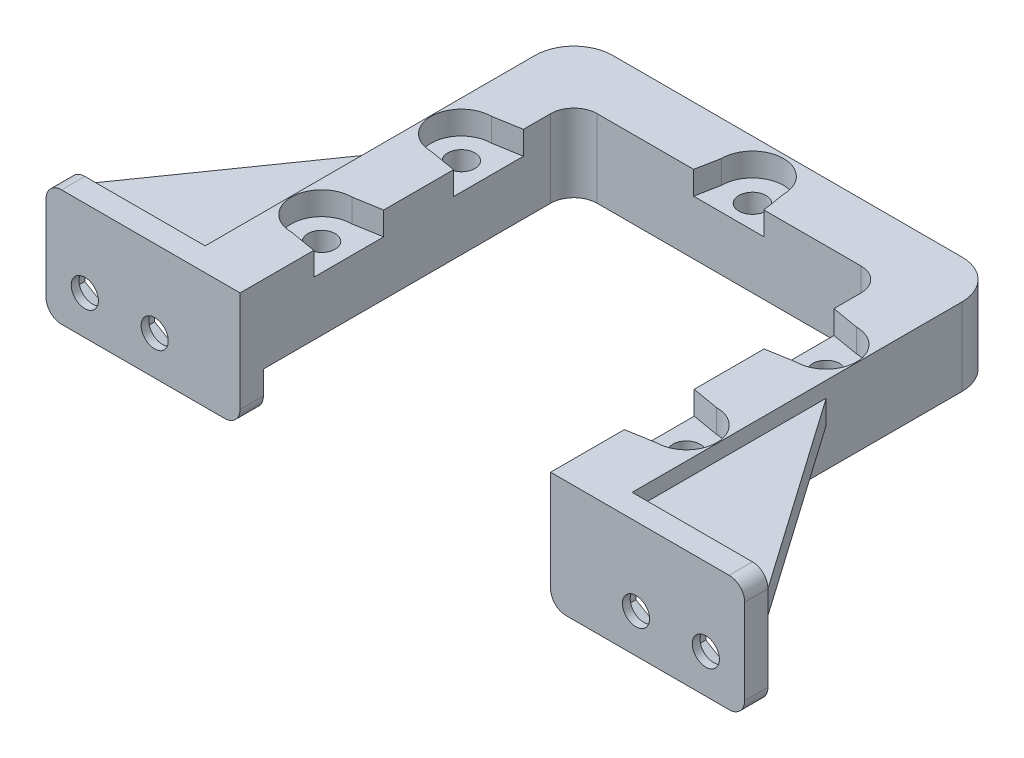
SolidWorks part; units mm, degrees
ref_plane "Front Plane" through (0, 0, 0) normal (0, 0, 1) x (1, 0, 0)
ref_plane "Top Plane" through (0, 0, 0) normal (0, 1, 0) x (1, 0, 0)
ref_plane "Right Plane" through (0, 0, 0) normal (1, 0, 0) x (0, 0, -1)
sketch "Sketch1" plane through (0, 0, 0) normal (0, 1, 0) x (1, 0, 0)
  line L0 (-20, -20) -> (-27.5, -20)
  line L1 (-17, 20) -> (17, 20)
  line L2 (-20, 17) -> (-20, -20)
  line L4 (20, 17) -> (20, -20)
  line L5 (-20, 20) -> (20, -20) construction
  line L6 (-20, -20) -> (20, 20) construction
  line L7 (-22.5, 27.5) -> (22.5, 27.5)
  line L8 (-27.5, 22.5) -> (-27.5, -20)
  line L10 (27.5, 22.5) -> (27.5, -20)
  line L11 (-27.5, 27.5) -> (27.5, -27.5) construction
  line L12 (-27.5, -27.5) -> (27.5, 27.5) construction
  line L13 (20, -20) -> (27.5, -20)
  line L14 (-20, -20) -> (20, -20) construction
  arc A0 (17, 20) -> (20, 17) centre (17, 17) cw
  arc A1 (-17, 20) -> (-20, 17) centre (-17, 17) ccw
  arc A2 (22.5, 27.5) -> (27.5, 22.5) centre (22.5, 22.5) cw
  arc A3 (-22.5, 27.5) -> (-27.5, 22.5) centre (-22.5, 22.5) ccw
  point P0 (0, 0)
  point P12 (0, 0)
  dimension "D3" = 3
  dimension "D6" = 5
  dimension "D1" = 40
  dimension "D2" = 40
  dimension "D4" = 55
  dimension "D5" = 55
  dimension "D9" = 7.5
extrude "Boss-Extrude1" add sketch "Sketch1" along normal blind 10
sketch "Sketch2" plane through (0, 10, 0) normal (0, 1, 0) x (1, 0, 0)
  line L0 (-23.5, -9) -> (23.5, -9) construction
  line L1 (0, -9) -> (0, -20) construction
  line L4 (-20, -20) -> (20, -20) construction
  line L5 (0, 20) -> (0, 23) construction
  line L6 (-17, 20) -> (17, 20) construction
  line L7 (-23.5, 9) -> (23.5, 9) construction
  line L8 (0, 9) -> (0, 20) construction
  circle A0 centre (-23.5, -9) radius 1.75
  circle A1 centre (23.5, -9) radius 1.75
  circle A2 centre (0, 23) radius 1.75
  circle A3 centre (-23.5, 9) radius 1.75
  circle A4 centre (23.5, 9) radius 1.75
  dimension "D3" = 3.5
  dimension "D4" = 3.5
  dimension "D6" = 3.5
  dimension "D9" = 3.5
  dimension "D10" = 3.5
  dimension "D1" = 11
  dimension "D2" = 47
  dimension "D5" = 3
  dimension "47" = 47
  dimension "D8" = 11
extrude "Cut-Extrude1" cut sketch "Sketch2" against normal blind 15.5
sketch "Sketch3" plane through (0, 0, 0) normal (0, -1, 0) x (1, 0, 0)
  line L1 (-20.6, 7.3257) -> (-20.6, 10.6743)
  line L2 (-20.6, 10.6743) -> (-23.5, 12.3486)
  line L3 (-23.5, 12.3486) -> (-26.4, 10.6743)
  line L4 (-26.4, 10.6743) -> (-26.4, 7.3257)
  line L5 (-26.4, 7.3257) -> (-23.5, 5.6514)
  line L6 (-23.5, 5.6514) -> (-20.6, 7.3257)
  line L7 (23.4997, 5.6514) -> (26.3998, 7.3254)
  line L8 (26.3998, 7.3254) -> (26.4002, 10.674)
  line L9 (26.4002, 10.674) -> (23.5003, 12.3486)
  line L10 (23.5003, 12.3486) -> (20.6002, 10.6746)
  line L11 (20.6002, 10.6746) -> (20.5998, 7.326)
  line L12 (20.5998, 7.326) -> (23.4997, 5.6514)
  line L13 (3.3486, -23) -> (1.6743, -20.1)
  line L14 (1.6743, -20.1) -> (-1.6743, -20.1)
  line L15 (-1.6743, -20.1) -> (-3.3486, -23)
  line L16 (-3.3486, -23) -> (-1.6743, -25.9)
  line L17 (-1.6743, -25.9) -> (1.6743, -25.9)
  line L18 (1.6743, -25.9) -> (3.3486, -23)
  line L19 (-23.4997, -5.6514) -> (-26.3998, -7.3254)
  line L20 (-26.3998, -7.3254) -> (-26.4002, -10.674)
  line L21 (-26.4002, -10.674) -> (-23.5003, -12.3486)
  line L22 (-23.5003, -12.3486) -> (-20.6002, -10.6746)
  line L23 (-20.6002, -10.6746) -> (-20.5998, -7.326)
  line L24 (-20.5998, -7.326) -> (-23.4997, -5.6514)
  line L25 (23.4997, -5.6514) -> (20.5998, -7.326)
  line L26 (20.5998, -7.326) -> (20.6002, -10.6746)
  line L27 (20.6002, -10.6746) -> (23.5003, -12.3486)
  line L28 (23.5003, -12.3486) -> (26.4002, -10.674)
  line L29 (26.4002, -10.674) -> (26.3998, -7.3254)
  line L30 (26.3998, -7.3254) -> (23.4997, -5.6514)
  circle A0 centre (-23.5, 9) radius 2.9 construction
  circle A1 centre (23.5, 9) radius 2.9 construction
  circle A2 centre (0, -23) radius 2.9 construction
  circle A3 centre (-23.5, -9) radius 2.9 construction
  circle A4 centre (23.5, -9) radius 2.9 construction
  dimension "D1" = 5.8
  dimension "D2" = 5.8
  dimension "D3" = 5.8
  dimension "D4" = 5.8
  dimension "D5" = 5.8
extrude "Cut-Extrude2" cut sketch "Sketch3" against normal blind 3
sketch "Sketch8" plane through (0, 10, 0) normal (0, 1, 0) x (1, 0, 0)
  line L0 (-4, 23) -> (-4.5746, 20)
  line L1 (-17, 20) -> (17, 20) construction
  line L2 (-4.5746, 20) -> (4.4783, 20)
  line L3 (4.4783, 20) -> (4, 23)
  line L4 (23.5, 12.9) -> (20, 13.5)
  line L5 (20, 17) -> (20, -20) construction
  line L6 (20, 13.5) -> (20, 4.5)
  line L7 (20, 4.5) -> (23.5, 5.1)
  line L8 (23.5, -5.1) -> (20, -4.5)
  line L9 (20, -4.5) -> (20, -13.5)
  line L10 (20, -13.5) -> (23.5, -12.9)
  line L11 (-23.5, -12.9) -> (-20, -13.5)
  line L12 (-20, -20) -> (-20, 17) construction
  line L13 (-20, -13.5) -> (-20, -4.5)
  line L14 (-20, -4.5) -> (-23.5, -5.1)
  line L15 (-20, -9) -> (-23.5, -9) construction
  line L16 (20, -9) -> (23.5, -9) construction
  line L17 (20, 9) -> (23.5, 9) construction
  line L18 (-0.0481, 20) -> (0, 23) construction
  line L19 (-23.5, 12.9) -> (-20, 13.5)
  line L20 (-20, 13.5) -> (-20, 4.5)
  line L21 (-20, 4.5) -> (-23.5, 5.1)
  line L22 (-23.5, 9) -> (-20, 9) construction
  arc A0 (4, 23) -> (-4, 23) centre (0, 23) ccw
  arc A1 (-23.5, 12.9) -> (-23.5, 5.1) centre (-23.5, 9) ccw
  arc A2 (-23.5, -5.1) -> (-23.5, -12.9) centre (-23.5, -9) ccw
  arc A4 (23.5, -12.9) -> (23.5, -5.1) centre (23.5, -9) ccw
  arc A5 (23.5, 5.1) -> (23.5, 12.9) centre (23.5, 9) ccw
  dimension "D1" = 9
  dimension "D2" = 9
  dimension "D3" = 9
  dimension "D4" = 9
extrude "Cut-Extrude7" cut sketch "Sketch8" against normal blind 3
sketch "Sketch9" plane through (0, 0, 20) normal (0, 0, 1) x (1, 0, 0)
  line L0 (-20, 10) -> (-20, -5)
  line L1 (-20, 10) -> (-45, 10)
  line L2 (-20, -5) -> (-45, -5)
  line L3 (-45, 10) -> (-45, -5)
  line L4 (-27.5, 10) -> (-27.5, 0) construction
  line L5 (-27.5, 0) -> (-20, 0) construction
  dimension "D1" = 25
  dimension "D2" = 15
  dimension "D3" = 7.5
  dimension "D4" = 5
extrude "Boss-Extrude2" add sketch "Sketch9" along normal blind 3
sketch "Sketch11" plane through (0, 0, 20) normal (0, 0, -1) x (-1, 0, 0)
  line L0 (45, 10) -> (45, -5) construction
  line L1 (45, 8) -> (27.5, 8)
  line L2 (45, 8) -> (45, 5)
  line L3 (45, 5) -> (27.5, 5)
  line L4 (27.5, 8) -> (27.5, 5)
  line L5 (27.5, 10) -> (27.5, 0) construction
  line L6 (45, -5) -> (20, -5) construction
  dimension "D1" = 3
  dimension "D2" = 10
extrude "Boss-Extrude4" add sketch "Sketch11" along normal blind 25
sketch "Sketch13" plane through (0, 5, 0) normal (0, -1, 0) x (1, 0, 0)
  line L0 (-45, 20) -> (-27.5, -5)
  line L1 (-27.5, -5) -> (-45, -5)
  line L2 (-45, -5) -> (-45, 20)
extrude "Cut-Extrude9" cut sketch "Sketch13" against normal blind 25
fillet "Fillet2" radius 2 3 edges at (-20, -5, 21.5) (-45, 10, 21.5) (-45, -5, 21.5)
sketch "Sketch14" plane through (0, 0, 20) normal (0, 0, -1) x (-1, 0, 0)
  line L0 (31, 0) -> (40, 0) construction
  line L1 (40, 0) -> (45, 0) construction
  line L2 (45, 5) -> (45, -3) construction
  circle A0 centre (40, 0) radius 1.75
  circle A1 centre (31, 0) radius 1.75
  dimension "D1" = 3.5
  dimension "D2" = 3.5
  dimension "D3" = 5
  dimension "D4" = 9
extrude "Cut-Extrude10" cut sketch "Sketch14" against normal through all
sketch "Sketch15" plane through (0, 0, 20) normal (0, 0, -1) x (-1, 0, 0)
  line L1 (31, 3.4641) -> (28, 1.7321)
  line L2 (28, 1.7321) -> (28, -1.7321)
  line L3 (28, -1.7321) -> (31, -3.4641)
  line L4 (31, -3.4641) -> (34, -1.7321)
  line L5 (34, -1.7321) -> (34, 1.7321)
  line L6 (34, 1.7321) -> (31, 3.4641)
  line L7 (40, 3.4641) -> (37, 1.7321)
  line L8 (37, 1.7321) -> (37, -1.7321)
  line L9 (37, -1.7321) -> (40, -3.4641)
  line L10 (40, -3.4641) -> (43, -1.7321)
  line L11 (43, -1.7321) -> (43, 1.7321)
  line L12 (43, 1.7321) -> (40, 3.4641)
  circle A0 centre (31, 0) radius 3 construction
  circle A1 centre (40, 0) radius 3 construction
  dimension "D1" = 6
  dimension "D2" = 6
extrude "Cut-Extrude11" cut sketch "Sketch15" against normal blind 2
mirror "Mirror1" about plane through (0, 0, 0) normal (1, 0, 0) of "Cut-Extrude11", "Cut-Extrude10", "Fillet2", "Cut-Extrude9", "Boss-Extrude4", "Boss-Extrude2"
